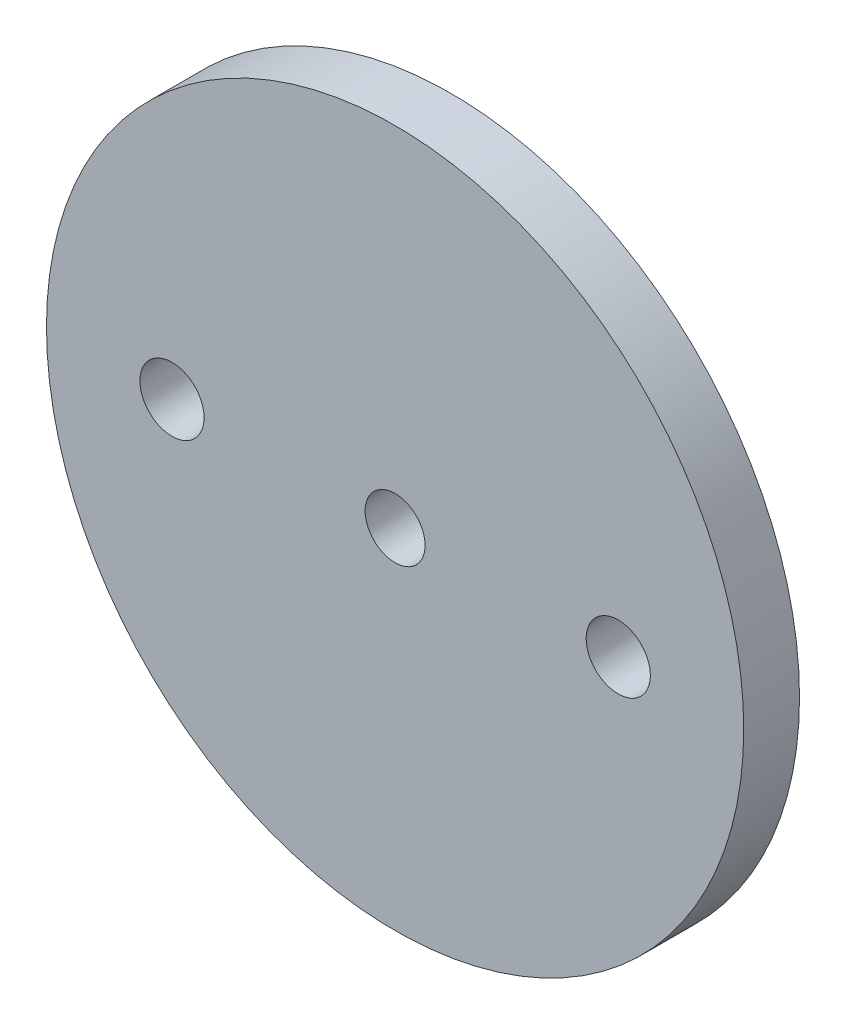
SolidWorks part; units mm, degrees
ref_plane "Front Plane" through (0, 0, 0) normal (0, 0, 1) x (1, 0, 0)
ref_plane "Top Plane" through (0, 0, 0) normal (0, 1, 0) x (1, 0, 0)
ref_plane "Right Plane" through (0, 0, 0) normal (1, 0, 0) x (0, 0, -1)
sketch "Sketch1" plane through (0, 0, 0) normal (0, 0, 1) x (1, 0, 0)
  line L0 (-1025, 0) -> (-12.5, 0) construction
  line L1 (0, 1001.7) -> (0, 12.5) construction
  line L2 (12.5, 0) -> (1012.5, 0) construction
  line L3 (0, -12.5) -> (0, -1012.5) construction
  circle A0 centre (0, 0) radius 12.5
  circle A1 centre (0, 0) radius 1.075
  circle A2 centre (-8, 0) radius 1.15
  circle A3 centre (8, 0) radius 1.15
  dimension "D1" = 25
  dimension "D2" = 2.15
  dimension "D3" = 2.3
  dimension "D4" = 8
extrude "Boss-Extrude1" add sketch "Sketch1" along normal blind 2
